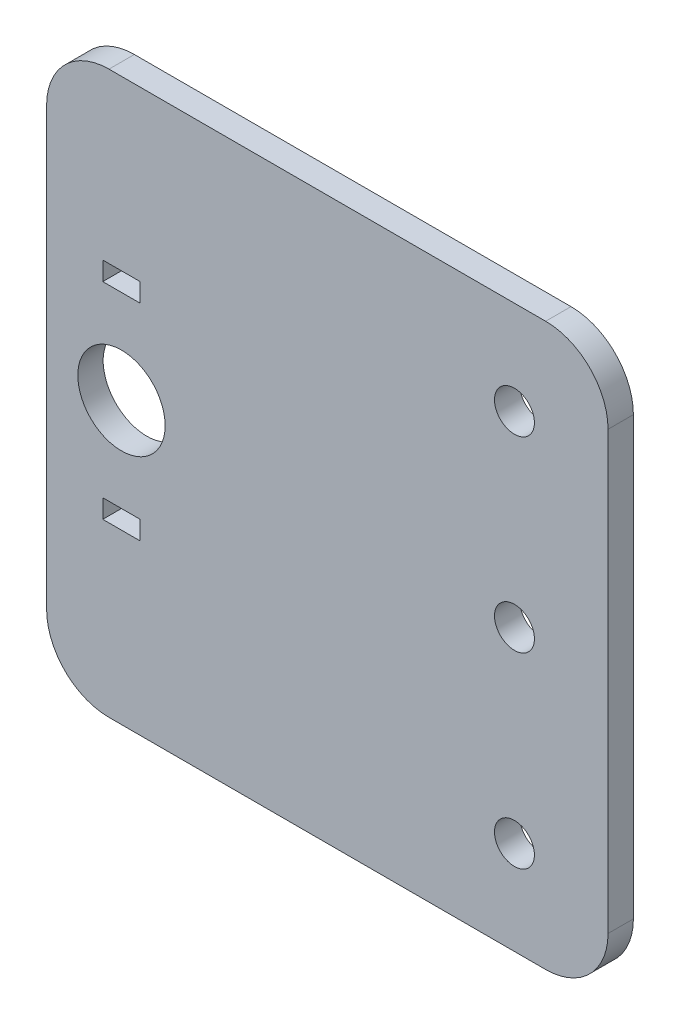
SolidWorks part; units mm, degrees
ref_plane "Front Plane" through (0, 0, 0) normal (0, 0, 1) x (1, 0, 0)
ref_plane "Top Plane" through (0, 0, 0) normal (0, 1, 0) x (1, 0, 0)
ref_plane "Right Plane" through (0, 0, 0) normal (1, 0, 0) x (0, 0, -1)
sketch "Sketch1" plane through (0, 0, 0) normal (0, 0, 1) x (1, 0, 0)
  line L0 (24, 22.5) -> (24, -22.5) construction
  line L1 (-6, -22.5) -> (39, -22.5)
  line L2 (-6, -22.5) -> (-6, 22.5)
  line L3 (-6, 22.5) -> (39, 22.5)
  line L4 (39, -22.5) -> (39, 22.5)
  line L13 (9, 22.5) -> (9, -22.5) construction
  circle A0 centre (0, 0) radius 3.5
  point P0 (0, 0)
  dimension "D2" = 7
  dimension "D1" = 6
  dimension "D5" = 45
  dimension "D6" = 15
  dimension "D7" = 15
extrude "Boss-Extrude1" add sketch "Sketch1" along normal blind 2.032
fillet "Fillet2" radius 5 4 edges at (39, 22.5, 1.016) (39, -22.5, 1.016) (-6, -22.5, 1.016) (-6, 22.5, 1.016)
sketch "Sketch2" [suppressed] plane through (0, 0, 2.032) normal (0, 0, 1) x (1, 0, 0)
  line L0 (0, 40.4519) -> (0, -37.5654) construction
  line L1 (0, -54.6431) -> (0, 54.6431) construction
  line L2 (47.3483, 0) -> (-47.3483, 0) construction
  line L3 (55, 0) -> (-55, 0) construction
  line L4 (-6, 17.5) -> (-6, -17.5) construction
  circle A0 centre (1.5, 0) radius 1.6
  circle A1 centre (1.5, 15) radius 1.6
  circle A2 centre (1.5, -15) radius 1.6
  circle A3 centre (-1.5, -15) radius 1.6
  circle A4 centre (-1.5, 15) radius 1.6
  circle A5 centre (-1.5, 0) radius 1.6
  dimension "D1" = 3.2
  dimension "D2" = 7.5
  dimension "D3" = 15
extrude "Cut-Extrude1" [suppressed] cut sketch "Sketch2" against normal through all
sketch "Sketch3" [suppressed] plane through (0, 0, 0) normal (0, 0, -1) x (-1, 0, 0)
  line L0 (-43.1144, 0) -> (46.045, 0) construction
  line L1 (0, 27.0792) -> (0, -27.3033) construction
  line L2 (-39, -17.5) -> (-39, 17.5) construction
  circle A0 centre (-34, 5) radius 1.6
  circle A1 centre (-34, -5) radius 1.6
  circle A2 centre (34, -5) radius 1.6
  circle A3 centre (34, 5) radius 1.6
  circle A4 centre (-30, -15) radius 1.6 construction
  point P15 (-30, -15)
  point P16 (-30, 15)
  dimension "D1" = 3.2
  dimension "D2" = 5
  dimension "D3" = 10
extrude "Cut-Extrude2" [suppressed] cut sketch "Sketch3" against normal through all
sketch "Alignment Sketch 1" [suppressed] plane through (0, 0, 2.032) normal (0, 0, 1) x (1, 0, 0)
  line L0 (-30, 15) -> (-30, -15) construction
  line L1 (30, 15) -> (30, -15) construction
  circle A0 centre (30, 15) radius 1.6 construction
  point P0 (-30, 15)
  point P1 (-30, 0)
  point P3 (-30, -15)
  point P5 (30, 15)
  point P7 (30, 0)
  point P8 (30, -15)
sketch "Sketch4" plane through (0, 0, 0) normal (0, 0, -1) x (-1, 0, 0)
  line L0 (-39, -17.5) -> (-39, 17.5) construction
  line L1 (-34, 22.5) -> (1, 22.5) construction
  line L2 (1, -22.5) -> (-34, -22.5) construction
  circle A0 centre (-31.5, 15) radius 1.6
  circle A1 centre (-31.5, 0) radius 1.6
  circle A2 centre (-31.5, -15) radius 1.6
  dimension "D1" = 3.2
  dimension "D2" = 7.5
  dimension "D3" = 7.5
  dimension "D4" = 7.5
  dimension "D5" = 7.5
  dimension "D6" = 7.5
  dimension "D7" = 15
  dimension "D8" = 15
extrude "Cut-Extrude3" cut sketch "Sketch4" against normal through all
sketch "Sketch5" plane through (0, 0, 0) normal (0, 0, -1) x (-1, 0, 0)
  line L0 (0, 8.25) -> (0, -8.25)
  line L1 (-1.5, 9) -> (1.5, 9)
  line L2 (-1.5, 9) -> (-1.5, 7.5)
  line L3 (-1.5, 7.5) -> (1.5, 7.5)
  line L4 (1.5, 9) -> (1.5, 7.5)
  line L5 (-1.5, 9) -> (1.5, 7.5) construction
  line L6 (-1.5, 7.5) -> (1.5, 9) construction
  line L7 (-1.5, -7.5) -> (1.5, -7.5)
  line L8 (-1.5, -7.5) -> (-1.5, -9)
  line L9 (-1.5, -9) -> (1.5, -9)
  line L10 (1.5, -7.5) -> (1.5, -9)
  line L11 (-1.5, -7.5) -> (1.5, -9) construction
  line L12 (-1.5, -9) -> (1.5, -7.5) construction
  circle A0 centre (0, 0) radius 3.5 construction
  point P0 (0, -8.25)
  dimension "D1" = 7.5
  dimension "D3" = 3
  dimension "D2" = 7.5
  dimension "D4" = 1.5
extrude "Cut-Extrude5" cut sketch "Sketch5" against normal through all contours L2 L3 L4 L1 | L8 L9 L10 L7
